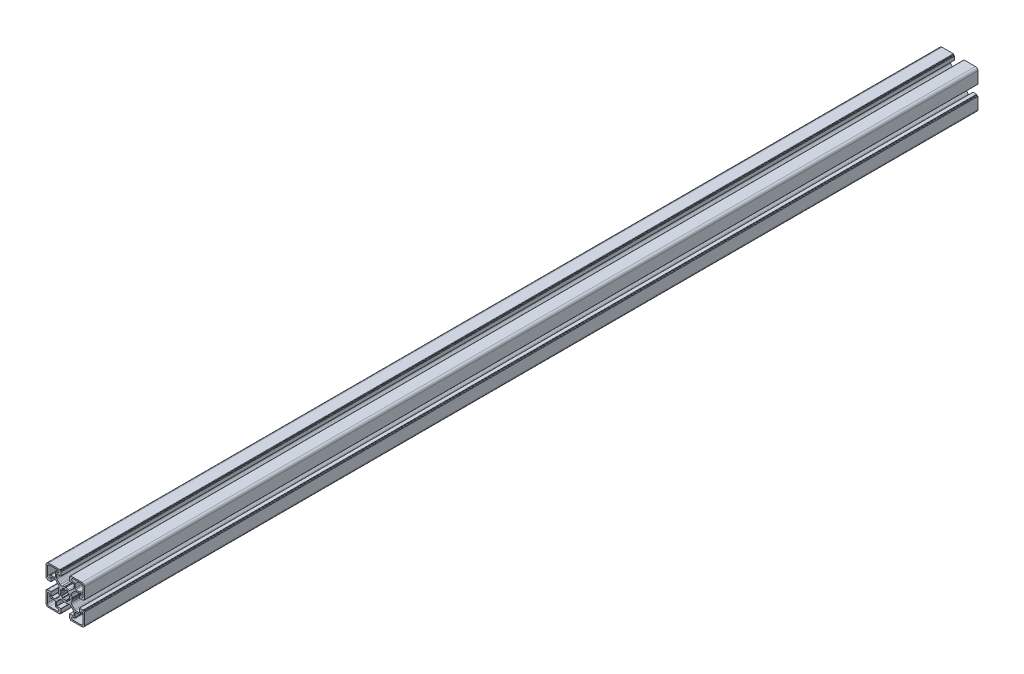
SolidWorks part; units mm, degrees
ref_plane "Plan de face" through (0, 0, 0) normal (0, 0, 1) x (1, 0, 0)
ref_plane "Plan de dessus" through (0, 0, 0) normal (0, 1, 0) x (1, 0, 0)
ref_plane "Plan de droite" through (0, 0, 0) normal (1, 0, 0) x (0, 0, -1)
sketch "Esquisse2" plane through (0, 0, 0) normal (0, 0, 1) x (1, 0, 0)
  line L28 (-195.0842, -352.0697) -> (-194.515, -352.1681)
  line L29 (-195.438, -354.39) -> (-195.9151, -354.0583)
  line L30 (-197.1408, -355.2803) -> (-196.8135, -355.7444)
  line L31 (-199.0372, -356.663) -> (-199.1374, -356.106)
  line L36 (-195.0842, -350.294) -> (-194.515, -350.1956)
  line L37 (-195.438, -347.9737) -> (-195.9151, -348.3053)
  line L38 (-197.1408, -347.0834) -> (-196.8135, -346.6192)
  line L39 (-199.0372, -345.7007) -> (-199.1374, -346.2577)
  line L40 (-200.9723, -356.663) -> (-200.8722, -356.106)
  line L41 (-202.8688, -355.2803) -> (-203.1961, -355.7444)
  line L42 (-204.5715, -354.39) -> (-204.0945, -354.0583)
  line L43 (-204.9253, -352.0697) -> (-205.4945, -352.1681)
  line L44 (-204.9253, -350.294) -> (-205.4945, -350.1956)
  line L45 (-204.5715, -347.9737) -> (-204.0945, -348.3053)
  line L46 (-202.8688, -347.0834) -> (-203.1961, -346.6192)
  line L47 (-200.9723, -345.7007) -> (-200.8722, -346.2577)
  line L105 (-200.0048, -338.2818) -> (-200.0048, -369.1677) construction
  line L107 (-190.0994, -351.1818) -> (-217.4619, -351.1818) construction
  line L108 (-191.0048, -330.1818) -> (-181.5048, -330.1818)
  line L109 (-189.4548, -333.1818) -> (-191.0048, -333.1818)
  line L116 (-221.0047, -332.6818) -> (-221.0047, -342.1816)
  line L117 (-218.0047, -342.1816) -> (-218.0047, -340.6318)
  line L118 (-217.0047, -339.6318) -> (-212.5547, -339.6318)
  line L119 (-211.5547, -338.6318) -> (-211.5547, -334.1818)
  line L120 (-210.5547, -333.1818) -> (-209.0047, -333.1818)
  line L121 (-209.0047, -330.1818) -> (-218.5047, -330.1818)
  line L122 (-188.4548, -338.6318) -> (-188.4548, -334.1818)
  line L123 (-183.0048, -339.6318) -> (-187.4548, -339.6318)
  line L124 (-182.0048, -342.1816) -> (-182.0048, -340.6318)
  line L125 (-179.0048, -332.6818) -> (-179.0048, -342.1816)
  line L126 (-191.0048, -372.1819) -> (-181.5048, -372.1819)
  line L127 (-189.4548, -369.1819) -> (-191.0048, -369.1819)
  line L128 (-188.4548, -363.7319) -> (-188.4548, -368.1819)
  line L129 (-183.0048, -362.7319) -> (-187.4548, -362.7319)
  line L130 (-182.0048, -360.182) -> (-182.0048, -361.7319)
  line L131 (-179.0048, -369.6819) -> (-179.0048, -360.182)
  line L196 (-192.4647, -351.135) -> (-192.0308, -350.3893)
  line L197 (-192.4413, -345.3231) -> (-188.875, -341.7569)
  line L198 (-187.5, -341.1873) -> (-183.6879, -341.1873)
  line L199 (-183.4879, -341.3873) -> (-183.4879, -345.9818)
  line L200 (-183.2879, -346.1818) -> (-179.2852, -346.1818)
  line L201 (-178.9852, -345.8818) -> (-178.9852, -345.6818)
  line L202 (-178.6852, -345.3818) -> (-178.0048, -345.3818)
  line L203 (-177.5048, -344.8818) -> (-177.5048, -331.6818)
  line L204 (-180.5048, -328.6818) -> (-193.6291, -328.6818)
  line L205 (-194.1291, -329.1818) -> (-194.1291, -329.8818)
  line L206 (-194.4291, -330.1818) -> (-194.7048, -330.1818)
  line L207 (-195.0048, -330.4818) -> (-195.0048, -334.515)
  line L208 (-194.8048, -334.715) -> (-190.0994, -334.715)
  line L209 (-189.8994, -334.915) -> (-189.8994, -338.7103)
  line L210 (-190.4852, -340.1245) -> (-194.0599, -343.6992)
  line L211 (-199.25, -343.207) -> (-199.8921, -343.5749)
  line L212 (-200.1174, -343.5749) -> (-200.7595, -343.207)
  line L213 (-205.9497, -343.6992) -> (-209.5244, -340.1245)
  line L214 (-210.1102, -338.7103) -> (-210.1102, -334.915)
  line L215 (-209.9102, -334.715) -> (-205.2048, -334.715)
  line L216 (-205.0048, -334.515) -> (-205.0048, -330.4818)
  line L217 (-205.3048, -330.1818) -> (-205.5805, -330.1818)
  line L218 (-205.8805, -329.8818) -> (-205.8805, -329.1818)
  line L219 (-206.3805, -328.6818) -> (-219.5047, -328.6818)
  line L220 (-222.5047, -331.6818) -> (-222.5047, -344.8818)
  line L221 (-222.0047, -345.3818) -> (-221.3244, -345.3818)
  line L222 (-221.0244, -345.6818) -> (-221.0244, -345.8818)
  line L223 (-220.7244, -346.1818) -> (-216.7217, -346.1818)
  line L224 (-216.5217, -345.9818) -> (-216.5217, -341.3873)
  line L225 (-216.3217, -341.1873) -> (-212.5095, -341.1873)
  line L226 (-211.1345, -341.7569) -> (-207.5682, -345.3231)
  line L227 (-207.9787, -350.3893) -> (-207.5448, -351.135)
  line L228 (-207.5448, -351.2287) -> (-207.9787, -351.9744)
  line L229 (-207.5682, -357.0405) -> (-211.1345, -360.6068)
  line L230 (-212.5095, -361.1764) -> (-216.3217, -361.1764)
  line L231 (-216.5217, -360.9764) -> (-216.5217, -356.3819)
  line L232 (-216.7217, -356.1819) -> (-220.7244, -356.1819)
  line L233 (-221.0244, -356.4819) -> (-221.0244, -356.6818)
  line L234 (-221.3244, -356.9818) -> (-222.0047, -356.9818)
  line L235 (-222.5047, -357.4818) -> (-222.5047, -370.6819)
  line L236 (-219.5047, -373.6819) -> (-206.3805, -373.6819)
  line L237 (-205.8805, -373.1819) -> (-205.8805, -372.4819)
  line L238 (-205.5805, -372.1819) -> (-205.3048, -372.1819)
  line L239 (-205.0048, -371.8819) -> (-205.0048, -367.8487)
  line L240 (-205.2048, -367.6487) -> (-209.9102, -367.6487)
  line L241 (-210.1102, -367.4487) -> (-210.1102, -363.6534)
  line L242 (-209.5244, -362.2392) -> (-205.9497, -358.6645)
  line L243 (-200.7595, -359.1566) -> (-200.1174, -358.7888)
  line L244 (-199.8921, -358.7888) -> (-199.25, -359.1566)
  line L245 (-194.0599, -358.6645) -> (-190.4852, -362.2392)
  line L246 (-189.8994, -363.6534) -> (-189.8994, -367.4487)
  line L247 (-190.0994, -367.6487) -> (-194.8048, -367.6487)
  line L248 (-195.0048, -367.8487) -> (-195.0048, -371.8819)
  line L249 (-194.7048, -372.1819) -> (-194.4291, -372.1819)
  line L250 (-194.1291, -372.4819) -> (-194.1291, -373.1819)
  line L251 (-193.6291, -373.6819) -> (-180.5048, -373.6819)
  line L252 (-177.5048, -370.6819) -> (-177.5048, -357.4818)
  line L253 (-178.0048, -356.9818) -> (-178.6852, -356.9818)
  line L254 (-178.9852, -356.6818) -> (-178.9852, -356.4819)
  line L255 (-179.2852, -356.1819) -> (-183.2879, -356.1819)
  line L256 (-183.4879, -356.3819) -> (-183.4879, -360.9764)
  line L257 (-183.6879, -361.1764) -> (-187.5, -361.1764)
  line L258 (-188.875, -360.6068) -> (-192.4413, -357.0405)
  line L259 (-192.0308, -351.9744) -> (-192.4647, -351.2287)
  line L260 (-209.0047, -372.1819) -> (-218.5047, -372.1819)
  line L261 (-210.5547, -369.1819) -> (-209.0047, -369.1819)
  line L262 (-211.5547, -363.7319) -> (-211.5547, -368.1819)
  line L263 (-217.0047, -362.7319) -> (-212.5547, -362.7319)
  line L264 (-218.0047, -360.182) -> (-218.0047, -361.7319)
  line L265 (-221.0047, -369.6819) -> (-221.0047, -360.182)
  arc A63 (-194.515, -352.1681) -> (-194.0979, -352.793) centre (-194.5809, -352.6637) cw
  arc A64 (-194.0979, -352.793) -> (-194.7023, -354.2383) centre (-199.9813, -351.1818) cw
  arc A65 (-194.7023, -354.2383) -> (-195.438, -354.39) centre (-195.1368, -353.9909) cw
  arc A66 (-195.9151, -354.0583) -> (-197.1408, -355.2803) centre (-200.0048, -351.1818) cw
  arc A67 (-196.8135, -355.7444) -> (-196.9604, -356.4813) centre (-197.2105, -356.0483) cw
  arc A68 (-196.9604, -356.4813) -> (-198.4097, -357.0759) centre (-199.9813, -351.1818) cw
  arc A69 (-198.4097, -357.0759) -> (-199.0372, -356.663) centre (-198.5421, -356.5938) cw
  arc A70 (-199.1374, -356.106) -> (-200.8722, -356.106) centre (-200.0048, -351.1818) cw
  arc A71 (-201.5998, -357.0759) -> (-200.9723, -356.663) centre (-201.4675, -356.5938) ccw
  arc A81 (-195.0842, -352.0697) -> (-195.0842, -350.294) centre (-200.0048, -351.1818) ccw
  arc A82 (-194.515, -350.1956) -> (-194.0979, -349.5706) centre (-194.5809, -349.7) ccw
  arc A83 (-194.0979, -349.5706) -> (-194.7023, -348.1254) centre (-199.9813, -351.1818) ccw
  arc A84 (-194.7023, -348.1254) -> (-195.438, -347.9737) centre (-195.1368, -348.3728) ccw
  arc A85 (-195.9151, -348.3053) -> (-197.1408, -347.0834) centre (-200.0048, -351.1818) ccw
  arc A86 (-196.8135, -346.6192) -> (-196.9604, -345.8824) centre (-197.2105, -346.3153) ccw
  arc A87 (-196.9604, -345.8824) -> (-198.4097, -345.2878) centre (-199.9813, -351.1818) ccw
  arc A88 (-198.4097, -345.2878) -> (-199.0372, -345.7007) centre (-198.5421, -345.7699) ccw
  arc A89 (-199.1374, -346.2577) -> (-200.8722, -346.2577) centre (-200.0048, -351.1818) ccw
  arc A90 (-203.0492, -356.4813) -> (-201.5998, -357.0759) centre (-200.0282, -351.1818) ccw
  arc A91 (-203.1961, -355.7444) -> (-203.0492, -356.4813) centre (-202.799, -356.0483) ccw
  arc A92 (-204.0945, -354.0583) -> (-202.8688, -355.2803) centre (-200.0048, -351.1818) ccw
  arc A93 (-205.3073, -354.2383) -> (-204.5715, -354.39) centre (-204.8728, -353.9909) ccw
  arc A94 (-205.9116, -352.793) -> (-205.3073, -354.2383) centre (-200.0282, -351.1818) ccw
  arc A95 (-205.4945, -352.1681) -> (-205.9116, -352.793) centre (-205.4286, -352.6637) ccw
  arc A96 (-204.9253, -352.0697) -> (-204.9253, -350.294) centre (-200.0048, -351.1818) cw
  arc A97 (-205.4945, -350.1956) -> (-205.9116, -349.5706) centre (-205.4286, -349.7) cw
  arc A98 (-205.9116, -349.5706) -> (-205.3073, -348.1254) centre (-200.0282, -351.1818) cw
  arc A99 (-205.3073, -348.1254) -> (-204.5715, -347.9737) centre (-204.8728, -348.3728) cw
  arc A100 (-204.0945, -348.3053) -> (-202.8688, -347.0834) centre (-200.0048, -351.1818) cw
  arc A101 (-203.1961, -346.6192) -> (-203.0492, -345.8824) centre (-202.799, -346.3153) cw
  arc A102 (-203.0492, -345.8824) -> (-201.5998, -345.2878) centre (-200.0282, -351.1818) cw
  arc A103 (-201.5998, -345.2878) -> (-200.9723, -345.7007) centre (-201.4675, -345.7699) cw
  arc A128 (-181.5048, -330.1818) -> (-179.0048, -332.6818) centre (-181.5048, -332.6818) cw
  arc A129 (-191.0048, -333.1818) -> (-191.0048, -330.1818) centre (-191.0048, -331.6818) cw
  arc A130 (-189.4548, -333.1818) -> (-188.4548, -334.1818) centre (-189.4548, -334.1818) cw
  arc A131 (-187.4548, -339.6318) -> (-188.4548, -338.6318) centre (-187.4548, -338.6318) cw
  arc A132 (-183.0048, -339.6318) -> (-182.0048, -340.6318) centre (-183.0048, -340.6318) cw
  arc A133 (-179.0048, -342.1816) -> (-182.0048, -342.1816) centre (-180.5048, -342.1816) cw
  arc A140 (-221.0047, -342.1816) -> (-218.0047, -342.1816) centre (-219.5047, -342.1816) ccw
  arc A141 (-217.0047, -339.6318) -> (-218.0047, -340.6318) centre (-217.0047, -340.6318) ccw
  arc A142 (-212.5547, -339.6318) -> (-211.5547, -338.6318) centre (-212.5547, -338.6318) ccw
  arc A143 (-210.5547, -333.1818) -> (-211.5547, -334.1818) centre (-210.5547, -334.1818) ccw
  arc A144 (-209.0047, -333.1818) -> (-209.0047, -330.1818) centre (-209.0047, -331.6818) ccw
  arc A145 (-218.5047, -330.1818) -> (-221.0047, -332.6818) centre (-218.5047, -332.6818) ccw
  arc A146 (-191.0048, -369.1819) -> (-191.0048, -372.1819) centre (-191.0048, -370.6819) ccw
  arc A147 (-189.4548, -369.1819) -> (-188.4548, -368.1819) centre (-189.4548, -368.1819) ccw
  arc A148 (-187.4548, -362.7319) -> (-188.4548, -363.7319) centre (-187.4548, -363.7319) ccw
  arc A149 (-183.0048, -362.7319) -> (-182.0048, -361.7319) centre (-183.0048, -361.7319) ccw
  arc A150 (-179.0048, -360.182) -> (-182.0048, -360.182) centre (-180.5048, -360.182) ccw
  arc A151 (-181.5048, -372.1819) -> (-179.0048, -369.6819) centre (-181.5048, -369.6819) ccw
  arc A152 (-218.5047, -372.1819) -> (-221.0047, -369.6819) centre (-218.5047, -369.6819) cw
  arc A153 (-209.0047, -369.1819) -> (-209.0047, -372.1819) centre (-209.0047, -370.6819) cw
  arc A154 (-210.5547, -369.1819) -> (-211.5547, -368.1819) centre (-210.5547, -368.1819) cw
  arc A155 (-212.5547, -362.7319) -> (-211.5547, -363.7319) centre (-212.5547, -363.7319) cw
  arc A156 (-217.0047, -362.7319) -> (-218.0047, -361.7319) centre (-217.0047, -361.7319) cw
  arc A157 (-221.0047, -360.182) -> (-218.0047, -360.182) centre (-219.5047, -360.182) cw
  arc A254 (-192.4647, -351.135) -> (-192.4734, -351.1818) centre (-192.2739, -351.1948) ccw
  arc A255 (-192.0308, -350.3893) -> (-192.0048, -350.2678) centre (-192.2037, -350.2887) ccw
  arc A256 (-192.0048, -350.2678) -> (-192.8044, -347.57) centre (-199.9552, -351.157) ccw
  arc A257 (-192.4413, -345.3231) -> (-192.8044, -347.57) centre (-191.0663, -346.6981) ccw
  arc A258 (-187.5, -341.1873) -> (-188.875, -341.7569) centre (-187.5, -343.1318) ccw
  arc A259 (-183.4879, -341.3873) -> (-183.6879, -341.1873) centre (-183.6879, -341.3873) ccw
  arc A260 (-183.4879, -345.9818) -> (-183.2879, -346.1818) centre (-183.2879, -345.9818) ccw
  arc A261 (-179.2852, -346.1818) -> (-178.9852, -345.8818) centre (-179.2852, -345.8818) ccw
  arc A262 (-178.6852, -345.3818) -> (-178.9852, -345.6818) centre (-178.6852, -345.6818) ccw
  arc A263 (-178.0048, -345.3818) -> (-177.5048, -344.8818) centre (-178.0048, -344.8818) ccw
  arc A264 (-177.5048, -331.6818) -> (-180.5048, -328.6818) centre (-180.5048, -331.6818) ccw
  arc A265 (-193.6291, -328.6818) -> (-194.1291, -329.1818) centre (-193.6291, -329.1818) ccw
  arc A266 (-194.4291, -330.1818) -> (-194.1291, -329.8818) centre (-194.4291, -329.8818) ccw
  arc A267 (-194.7048, -330.1818) -> (-195.0048, -330.4818) centre (-194.7048, -330.4818) ccw
  arc A268 (-195.0048, -334.515) -> (-194.8048, -334.715) centre (-194.8048, -334.515) ccw
  arc A269 (-189.8994, -334.915) -> (-190.0994, -334.715) centre (-190.0994, -334.915) ccw
  arc A270 (-190.4852, -340.1245) -> (-189.8994, -338.7103) centre (-191.8994, -338.7103) ccw
  arc A271 (-196.3383, -344.0086) -> (-194.0599, -343.6992) centre (-195.4193, -342.2322) ccw
  arc A272 (-196.3383, -344.0086) -> (-199.1284, -343.1818) centre (-199.9813, -351.1818) ccw
  arc A273 (-199.1284, -343.1818) -> (-199.25, -343.207) centre (-199.1506, -343.3806) ccw
  arc A274 (-200.0048, -343.6509) -> (-199.8921, -343.5749) centre (-200.0537, -343.457) ccw
  arc A275 (-200.1174, -343.5749) -> (-200.0048, -343.6509) centre (-199.9559, -343.457) ccw
  arc A276 (-200.7595, -343.207) -> (-200.8812, -343.1818) centre (-200.8589, -343.3806) ccw
  arc A277 (-200.8812, -343.1818) -> (-203.6713, -344.0086) centre (-200.0282, -351.1818) ccw
  arc A278 (-205.9497, -343.6992) -> (-203.6713, -344.0086) centre (-204.5903, -342.2322) ccw
  arc A279 (-210.1102, -338.7103) -> (-209.5244, -340.1245) centre (-208.1102, -338.7103) ccw
  arc A280 (-209.9102, -334.715) -> (-210.1102, -334.915) centre (-209.9102, -334.915) ccw
  arc A281 (-205.2048, -334.715) -> (-205.0048, -334.515) centre (-205.2048, -334.515) ccw
  arc A282 (-205.0048, -330.4818) -> (-205.3048, -330.1818) centre (-205.3048, -330.4818) ccw
  arc A283 (-205.8805, -329.8818) -> (-205.5805, -330.1818) centre (-205.5805, -329.8818) ccw
  arc A284 (-205.8805, -329.1818) -> (-206.3805, -328.6818) centre (-206.3805, -329.1818) ccw
  arc A285 (-219.5047, -328.6818) -> (-222.5047, -331.6818) centre (-219.5047, -331.6818) ccw
  arc A286 (-222.5047, -344.8818) -> (-222.0047, -345.3818) centre (-222.0047, -344.8818) ccw
  arc A287 (-221.0244, -345.6818) -> (-221.3244, -345.3818) centre (-221.3244, -345.6818) ccw
  arc A288 (-221.0244, -345.8818) -> (-220.7244, -346.1818) centre (-220.7244, -345.8818) ccw
  arc A289 (-216.7217, -346.1818) -> (-216.5217, -345.9818) centre (-216.7217, -345.9818) ccw
  arc A290 (-216.3217, -341.1873) -> (-216.5217, -341.3873) centre (-216.3217, -341.3873) ccw
  arc A291 (-211.1345, -341.7569) -> (-212.5095, -341.1873) centre (-212.5095, -343.1318) ccw
  arc A292 (-207.2051, -347.57) -> (-207.5682, -345.3231) centre (-208.9432, -346.6981) ccw
  arc A293 (-207.2051, -347.57) -> (-208.0048, -350.2678) centre (-200.0543, -351.157) ccw
  arc A294 (-208.0048, -350.2678) -> (-207.9787, -350.3893) centre (-207.8059, -350.2887) ccw
  arc A295 (-207.5361, -351.1818) -> (-207.5448, -351.135) centre (-207.7357, -351.1948) ccw
  arc A296 (-207.5448, -351.2287) -> (-207.5361, -351.1818) centre (-207.7357, -351.1689) ccw
  arc A297 (-207.9787, -351.9744) -> (-208.0048, -352.0959) centre (-207.8059, -352.075) ccw
  arc A298 (-208.0048, -352.0959) -> (-207.2051, -354.7937) centre (-200.0543, -351.2067) ccw
  arc A299 (-207.5682, -357.0405) -> (-207.2051, -354.7937) centre (-208.9432, -355.6656) ccw
  arc A300 (-212.5095, -361.1764) -> (-211.1345, -360.6068) centre (-212.5095, -359.2319) ccw
  arc A301 (-216.5217, -360.9764) -> (-216.3217, -361.1764) centre (-216.3217, -360.9764) ccw
  arc A302 (-216.5217, -356.3819) -> (-216.7217, -356.1819) centre (-216.7217, -356.3819) ccw
  arc A303 (-220.7244, -356.1819) -> (-221.0244, -356.4819) centre (-220.7244, -356.4819) ccw
  arc A304 (-221.3244, -356.9818) -> (-221.0244, -356.6818) centre (-221.3244, -356.6818) ccw
  arc A305 (-222.0047, -356.9818) -> (-222.5047, -357.4818) centre (-222.0047, -357.4818) ccw
  arc A306 (-222.5047, -370.6819) -> (-219.5047, -373.6819) centre (-219.5047, -370.6819) ccw
  arc A307 (-206.3805, -373.6819) -> (-205.8805, -373.1819) centre (-206.3805, -373.1819) ccw
  arc A308 (-205.5805, -372.1819) -> (-205.8805, -372.4819) centre (-205.5805, -372.4819) ccw
  arc A309 (-205.3048, -372.1819) -> (-205.0048, -371.8819) centre (-205.3048, -371.8819) ccw
  arc A310 (-205.0048, -367.8487) -> (-205.2048, -367.6487) centre (-205.2048, -367.8487) ccw
  arc A311 (-210.1102, -367.4487) -> (-209.9102, -367.6487) centre (-209.9102, -367.4487) ccw
  arc A312 (-209.5244, -362.2392) -> (-210.1102, -363.6534) centre (-208.1102, -363.6534) ccw
  arc A313 (-203.6713, -358.3551) -> (-205.9497, -358.6645) centre (-204.5903, -360.1315) ccw
  arc A314 (-203.6713, -358.3551) -> (-200.8812, -359.1819) centre (-200.0282, -351.1818) ccw
  arc A315 (-200.8812, -359.1819) -> (-200.7595, -359.1566) centre (-200.8589, -358.9831) ccw
  arc A316 (-200.0048, -358.7128) -> (-200.1174, -358.7888) centre (-199.9559, -358.9067) ccw
  arc A317 (-199.8921, -358.7888) -> (-200.0048, -358.7128) centre (-200.0537, -358.9067) ccw
  arc A318 (-199.25, -359.1566) -> (-199.1284, -359.1819) centre (-199.1506, -358.9831) ccw
  arc A319 (-199.1284, -359.1819) -> (-196.3383, -358.3551) centre (-199.9813, -351.1818) ccw
  arc A320 (-194.0599, -358.6645) -> (-196.3383, -358.3551) centre (-195.4193, -360.1315) ccw
  arc A321 (-189.8994, -363.6534) -> (-190.4852, -362.2392) centre (-191.8994, -363.6534) ccw
  arc A322 (-190.0994, -367.6487) -> (-189.8994, -367.4487) centre (-190.0994, -367.4487) ccw
  arc A323 (-194.8048, -367.6487) -> (-195.0048, -367.8487) centre (-194.8048, -367.8487) ccw
  arc A324 (-195.0048, -371.8819) -> (-194.7048, -372.1819) centre (-194.7048, -371.8819) ccw
  arc A325 (-194.1291, -372.4819) -> (-194.4291, -372.1819) centre (-194.4291, -372.4819) ccw
  arc A326 (-194.1291, -373.1819) -> (-193.6291, -373.6819) centre (-193.6291, -373.1819) ccw
  arc A327 (-180.5048, -373.6819) -> (-177.5048, -370.6819) centre (-180.5048, -370.6819) ccw
  arc A328 (-177.5048, -357.4818) -> (-178.0048, -356.9818) centre (-178.0048, -357.4818) ccw
  arc A329 (-178.9852, -356.6818) -> (-178.6852, -356.9818) centre (-178.6852, -356.6818) ccw
  arc A330 (-178.9852, -356.4819) -> (-179.2852, -356.1819) centre (-179.2852, -356.4819) ccw
  arc A331 (-183.2879, -356.1819) -> (-183.4879, -356.3819) centre (-183.2879, -356.3819) ccw
  arc A332 (-183.6879, -361.1764) -> (-183.4879, -360.9764) centre (-183.6879, -360.9764) ccw
  arc A333 (-188.875, -360.6068) -> (-187.5, -361.1764) centre (-187.5, -359.2319) ccw
  arc A334 (-192.8044, -354.7937) -> (-192.4413, -357.0405) centre (-191.0663, -355.6656) ccw
  arc A335 (-192.8044, -354.7937) -> (-192.0048, -352.0959) centre (-199.9552, -351.2067) ccw
  arc A336 (-192.0048, -352.0959) -> (-192.0308, -351.9744) centre (-192.2037, -352.075) ccw
  arc A337 (-192.4734, -351.1818) -> (-192.4647, -351.2287) centre (-192.2739, -351.1689) ccw
extrude "Boss.-Extru.1" add sketch "Esquisse2" along normal blind 1045
